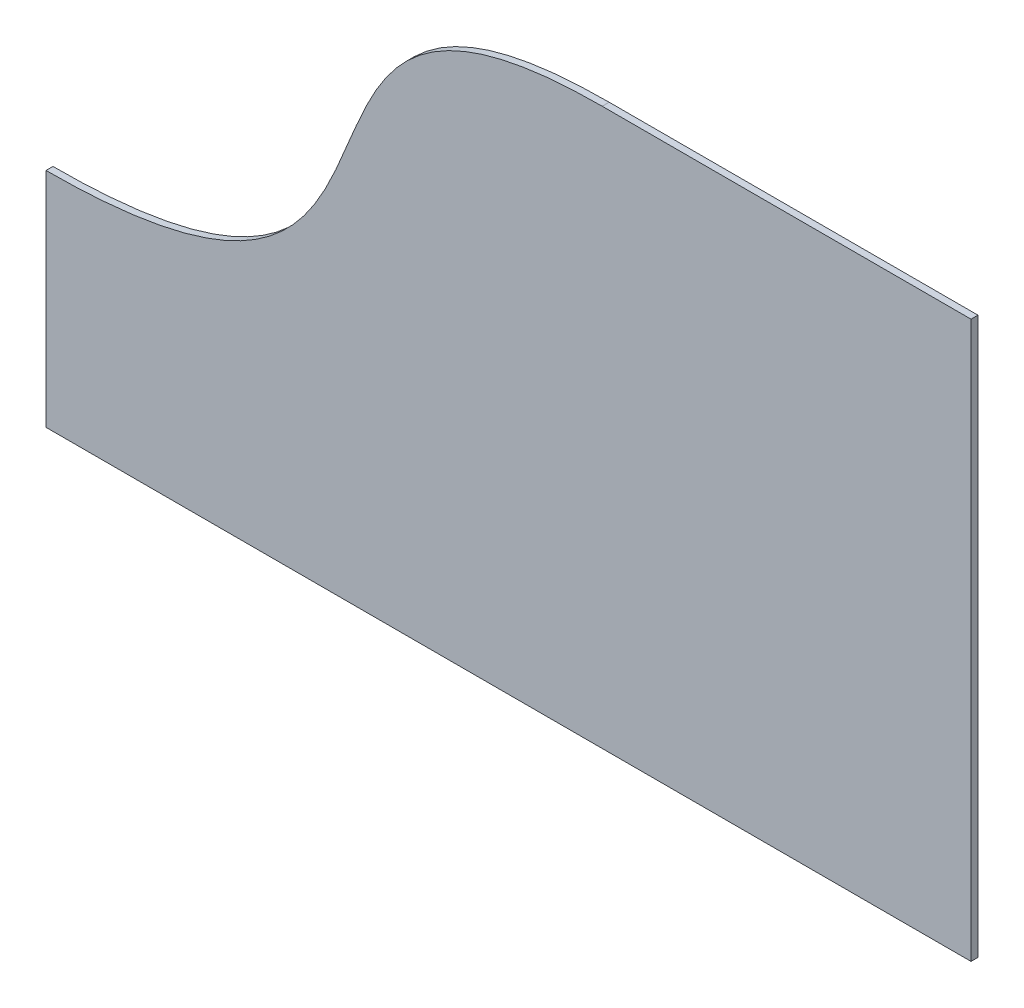
SolidWorks part; units mm, degrees
ref_plane "Front Plane" through (0, 0, 0) normal (0, 0, 1) x (1, 0, 0)
ref_plane "Top Plane" through (0, 0, 0) normal (0, 1, 0) x (1, 0, 0)
ref_plane "Right Plane" through (0, 0, 0) normal (1, 0, 0) x (0, 0, -1)
sketch "Sketch1" plane through (0, 0, 0) normal (0, 0, 1) x (1, 0, 0)
  line L0 (149.6477, 213.342) -> (-18.7823, 213.342)
  line L3 (-272.7823, -40.658) -> (149.6477, -40.658)
  line L4 (149.6477, 213.342) -> (149.6477, -40.658)
  line L7 (-272.7823, -40.658) -> (-272.7823, 60.942)
  line L8 (-272.7823, -40.658) -> (-272.7823, 249.41) construction
  line L10 (-18.7823, 213.342) -> (-196.5823, 213.342) construction
  line L11 (-196.5823, 213.342) -> (-69.5823, 60.942) construction
  line L12 (-69.5823, 60.942) -> (-272.7823, 60.942) construction
  spline S1 degree 3 poles (-18.7823, 213.342) (-196.5823, 213.342) (-69.5823, 60.942) (-272.7823, 60.942) knots 0 0 0 0 1 1 1 1
  dimension "D1" = 177.8
  dimension "D2" = 203.2
extrude "Boss-Extrude1" add sketch "Sketch1" along normal blind 3.175
